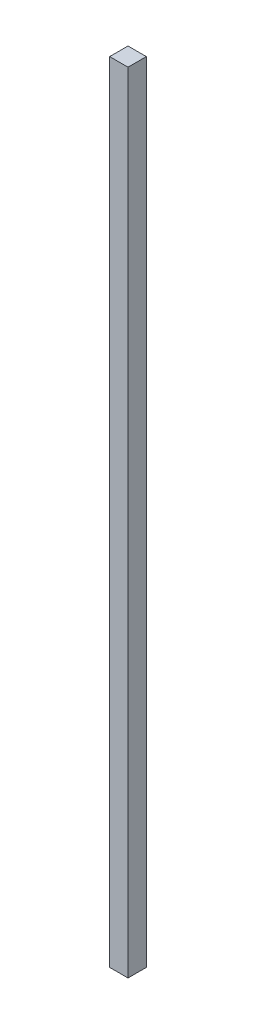
SolidWorks part; units mm, degrees
ref_plane "Front Plane" through (0, 0, 0) normal (0, 0, 1) x (1, 0, 0)
ref_plane "Top Plane" through (0, 0, 0) normal (0, 1, 0) x (1, 0, 0)
ref_plane "Right Plane" through (0, 0, 0) normal (1, 0, 0) x (0, 0, -1)
sketch "Sketch1" plane through (0, 0, 0) normal (0, 1, 0) x (1, 0, 0)
  line L1 (0, 0) -> (20, 0)
  line L2 (0, 0) -> (0, -20)
  line L3 (0, -20) -> (20, -20)
  line L4 (20, 0) -> (20, -20)
extrude "Boss-Extrude1" add sketch "Sketch1" along normal blind 860
